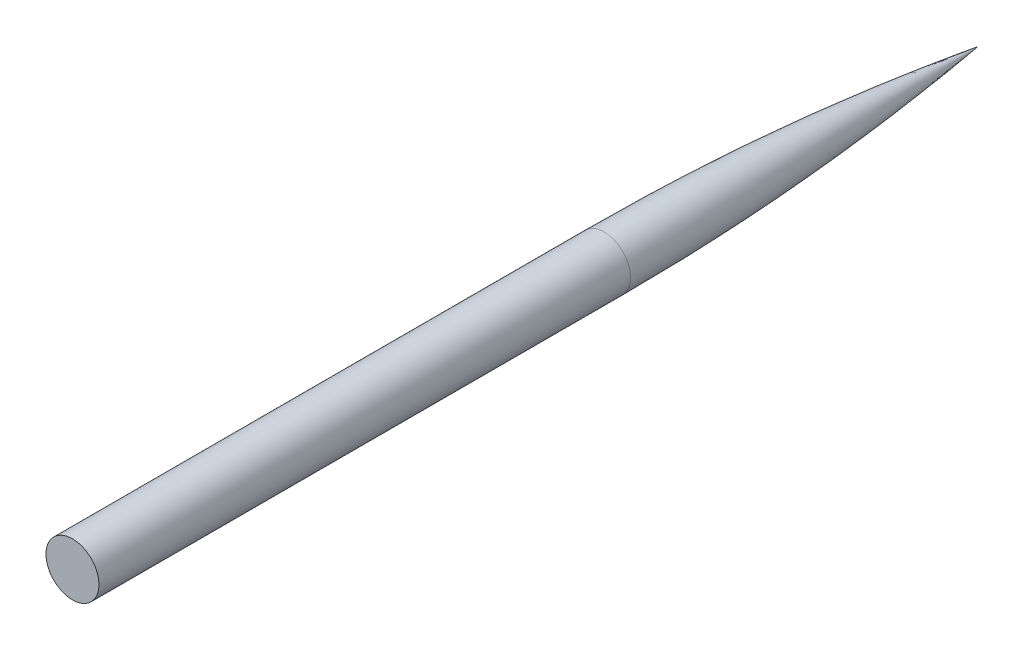
SolidWorks part; units mm, degrees
ref_plane "Front Plane" through (0, 0, 0) normal (0, 0, 1) x (1, 0, 0)
ref_plane "Top Plane" through (0, 0, 0) normal (0, 1, 0) x (1, 0, 0)
ref_plane "Right Plane" through (0, 0, 0) normal (1, 0, 0) x (0, 0, -1)
sketch "Sketch1" plane through (0, 0, 0) normal (0, 1, 0) x (1, 0, 0)
  line L0 (0, 60.1744) -> (0, -25) construction
  line L3 (0, -25) -> (2.49, -25)
  line L4 (2.49, 25) -> (2.49, -25)
  line L5 (0, -25) -> (0, 60.1744)
  arc A3 (2.49, 25) -> (0, 60.1744) centre (-247.1961, 25) ccw
  point P0 (0, 0)
  point P6 (0, -25)
  dimension "D2" = 50
revolve "Revolve2" add sketch "Sketch1" angle 360 about L0
